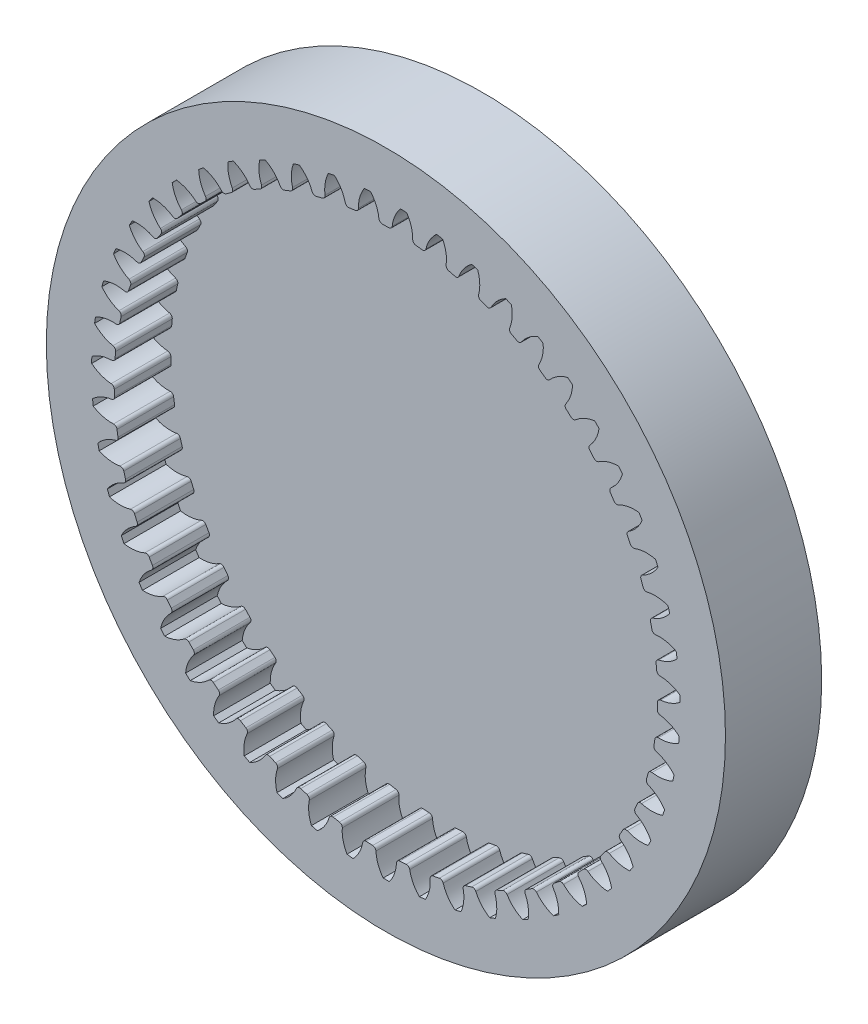
SolidWorks part; units mm, degrees
ref_plane "Front Plane" through (0, 0, 0) normal (0, 0, 1) x (1, 0, 0)
ref_plane "Top Plane" through (0, 0, 0) normal (0, 1, 0) x (1, 0, 0)
ref_plane "Right Plane" through (0, 0, 0) normal (1, 0, 0) x (0, 0, -1)
sketch "Sketch1" plane through (0, 0, 0) normal (0, 0, 1) x (1, 0, 0)
  circle A0 centre (0, 0) radius 60
  dimension "D1" = 120
extrude "Boss-Extrude1" add sketch "Sketch1" along normal blind 10
sketch "Sketch5" plane through (0, 0, 0) normal (0, 0, -1) x (-1, 0, 0)
  arc A1 (2.7166, 51.929) -> (1.2312, 48.5289) centre (7.4674, 47.829) ccw
  arc A2 (3.8132, 51.86) -> (2.7166, 51.929) centre (0, 0) ccw
  arc A3 (5.3933, 47.696) -> (0.6271, 47.9959) centre (0, 0) ccw
  circle A5 centre (0, 0) radius 48 construction
  arc A8 (4.8608, 48.3006) -> (5.3933, 47.696) centre (5.4607, 48.2922) ccw
  arc A9 (0.6271, 47.9959) -> (1.2312, 48.5289) centre (0.635, 48.5959) ccw
  arc A12 (4.8608, 48.3006) -> (3.8132, 51.86) centre (-1.414, 48.3878) ccw
  dimension "D1" = 96
extrude "Cut-Extrude2" cut sketch "Sketch5" against normal through all
pattern_circular "CirPattern2" count 51 over 360 about axis through (0, 0, 0) along (0, 0, 1) of "Cut-Extrude2"
sketch "Sketch6" plane through (0, 0, 0) normal (0, 0, -1) x (-1, 0, 0)
  circle A0 centre (0, 0) radius 48
  dimension "D1" = 96
extrude "Cut-Extrude3" cut sketch "Sketch6" against normal through all
sketch "Sketch8" plane through (0, 0, 0) normal (0, 0, -1) x (-1, 0, 0)
  circle A0 centre (0, 0) radius 60
extrude "Boss-Extrude3" add sketch "Sketch8" along normal blind 7
sketch "Sketch9" plane through (0, 0, -7) normal (0, 0, -1) x (-1, 0, 0)
  line L0 (-9.463, -3.2328) -> (1.316, 9.913)
  arc A0 (-9.463, -3.2328) -> (1.316, 9.913) centre (0, 0) ccw
  dimension "D1" = 20
  dimension "D2" = 17
extrude "Cut-Extrude4" cut sketch "Sketch9" against normal blind 6
